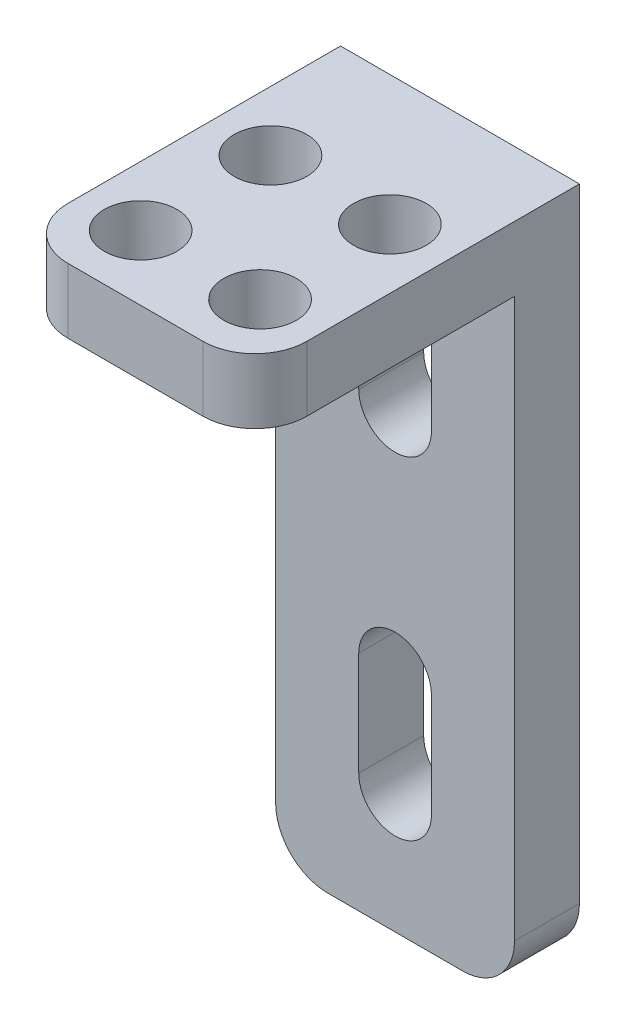
SolidWorks part; units mm, degrees
ref_plane "Front Plane" through (0, 0, 0) normal (0, 0, 1) x (1, 0, 0)
ref_plane "Top Plane" through (0, 0, 0) normal (0, 1, 0) x (1, 0, 0)
ref_plane "Right Plane" through (0, 0, 0) normal (1, 0, 0) x (0, 0, -1)
sketch "Sketch1" plane through (0, 0, 0) normal (0, 0, 1) x (1, 0, 0)
  line L0 (0.0217, 16.51) -> (0.0217, -16.51) construction
  line L1 (5.8637, -16.51) -> (-5.8203, -16.51)
  line L2 (5.8637, -16.51) -> (5.8637, 16.51)
  line L3 (5.8637, 16.51) -> (-5.8203, 16.51)
  line L4 (-5.8203, -16.51) -> (-5.8203, 16.51)
  line L6 (1.7997, 5.5188) -> (1.5002, 4.6004) construction
  line L7 (0.0217, 5.588) -> (0.0217, 10.668) construction
  line L8 (-1.7563, 5.588) -> (-1.7563, 10.668)
  line L9 (1.7997, 5.588) -> (1.7997, 10.668)
  line L10 (5.8203, 0) -> (-5.8203, 0) construction
  line L13 (0.0217, -5.588) -> (0.0217, -10.668) construction
  line L14 (-1.7563, -5.588) -> (-1.7563, -10.668)
  line L15 (1.7997, -5.588) -> (1.7997, -10.668)
  arc A1 (-1.7563, 5.588) -> (1.7997, 5.588) centre (0.0217, 5.588) ccw
  arc A2 (1.7997, 10.668) -> (-1.7563, 10.668) centre (0.0217, 10.668) ccw
  arc A5 (-1.7563, -5.588) -> (1.7997, -5.588) centre (0.0217, -5.588) cw
  arc A6 (1.7997, -10.668) -> (-1.7563, -10.668) centre (0.0217, -10.668) cw
  point P0 (0, 0)
  point P8 (0.0217, 8.128)
  point P13 (0.0217, 8.128)
  point P19 (0, 0)
  point P21 (0.0217, -8.128)
  dimension "D3" = 8.382
  dimension "D4" = 1.778
  dimension "D1" = 11.684
  dimension "D2" = 33.02
  dimension ".26" = 5.08
extrude "Boss-Extrude1" add sketch "Sketch1" along normal blind 3.175
sketch "Sketch2" plane through (0, 0, 3.175) normal (0, 0, 1) x (1, 0, 0)
  line L0 (5.8637, -16.51) -> (5.8637, 16.51) construction
  line L1 (-5.8203, 16.51) -> (5.8637, 16.51)
  line L2 (-5.8203, 16.51) -> (-5.8203, 13.335)
  line L3 (-5.8203, 13.335) -> (5.8637, 13.335)
  line L4 (5.8637, 16.51) -> (5.8637, 13.335)
  dimension "D1" = 3.175
extrude "Boss-Extrude2" add sketch "Sketch2" along normal blind 12.7
sketch "Sketch3" plane through (0, 16.51, 0) normal (0, 1, 0) x (1, 0, 0)
  line L0 (-5.8203, 0) -> (-5.8203, -3.175) construction
  line L3 (-5.8203, -15.875) -> (-5.8203, 0) construction
  line L5 (-5.8203, -3.175) -> (5.8637, -3.175) construction
  line L6 (-5.8203, -3.175) -> (-5.8203, -15.875) construction
  line L7 (-5.8203, -15.875) -> (5.8637, -15.875) construction
  line L8 (5.8637, -15.875) -> (5.8637, -3.175) construction
  line L9 (0.0217, -3.175) -> (0.0217, -15.875) construction
  line L10 (-5.8203, -9.525) -> (5.8637, -9.525) construction
  line L11 (0.0217, -3.175) -> (-5.8203, -9.525) construction
  line L12 (-5.8203, -3.175) -> (0.0217, -9.525) construction
  circle A5 centre (-2.8993, -6.35) radius 1.778
  circle A6 centre (2.9427, -6.35) radius 1.778
  circle A7 centre (-2.8993, -12.7) radius 1.778
  circle A8 centre (2.9427, -12.7) radius 1.778
  dimension "D1" = 3.175
  dimension "D2" = 3.556
  dimension "D3" = 5.842
  dimension "D4" = 6.35
  dimension "D5" = 6.35
extrude "Cut-Extrude2" cut sketch "Sketch3" against normal up to next
fillet "Fillet2" radius 2.54 4 edges at (5.8637, -16.51, 1.5875) (5.8637, 14.9225, 15.875) (-5.8203, 14.9225, 15.875) (-5.8203, -16.51, 1.5875)
